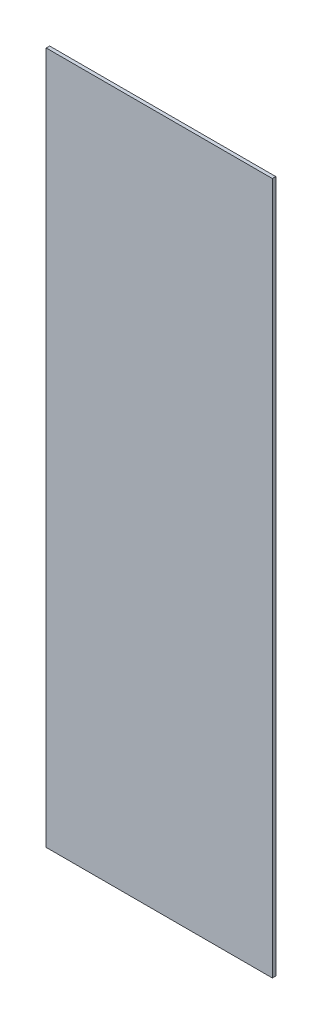
SolidWorks part; units mm, degrees
ref_plane "Plan de face" through (0, 0, 0) normal (0, 0, 1) x (1, 0, 0)
ref_plane "Plan de dessus" through (0, 0, 0) normal (0, 1, 0) x (1, 0, 0)
ref_plane "Plan de droite" through (0, 0, 0) normal (1, 0, 0) x (0, 0, -1)
sketch "Esquisse1" plane through (0, 0, 0) normal (0, 0, 1) x (1, 0, 0)
  line L1 (-311.9094, 134.7595) -> (18.0906, 134.7595)
  line L2 (-311.9094, 134.7595) -> (-311.9094, -875.7405)
  line L3 (-311.9094, -875.7405) -> (18.0906, -875.7405)
  line L4 (18.0906, 134.7595) -> (18.0906, -875.7405)
  dimension "D1" = 330
  dimension "D2" = 1010.5
extrude "Boss.-Extru.1" add sketch "Esquisse1" along normal blind 5
